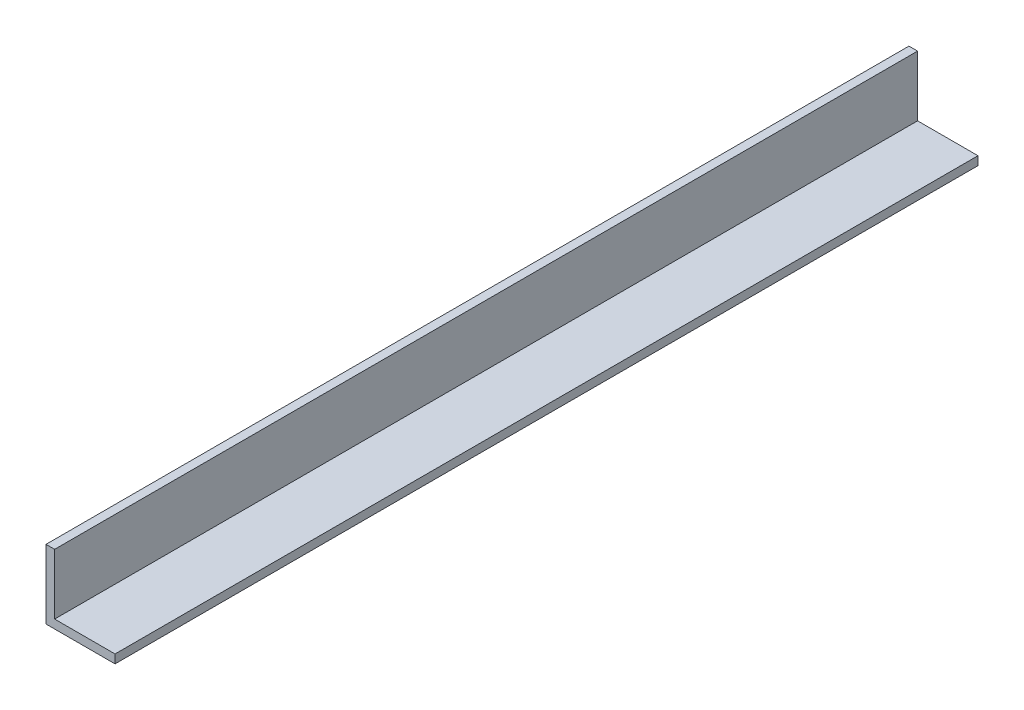
SolidWorks part; units mm, degrees
material "1060 Alloy"
ref_plane "Front Plane" through (0, 0, 0) normal (0, 0, 1) x (1, 0, 0)
ref_plane "Top Plane" through (0, 0, 0) normal (0, 1, 0) x (1, 0, 0)
ref_plane "Right Plane" through (0, 0, 0) normal (1, 0, 0) x (0, 0, -1)
sketch "Sketch1" plane through (0, 0, 0) normal (0, 0, 1) x (1, 0, 0)
  line L1 (0, 0) -> (25.4, 0)
  line L2 (0, 0) -> (0, 25.4)
  line L3 (0, 25.4) -> (3.175, 25.4)
  line L4 (25.4, 0) -> (25.4, 3.175)
  line L7 (25.4, 3.175) -> (3.175, 3.175)
  line L8 (3.175, 25.4) -> (3.175, 3.175)
  dimension "D1" = 3.175
  dimension "D2" = 25.4
extrude "Boss-Extrude1" add sketch "Sketch1" along normal blind 317.5
